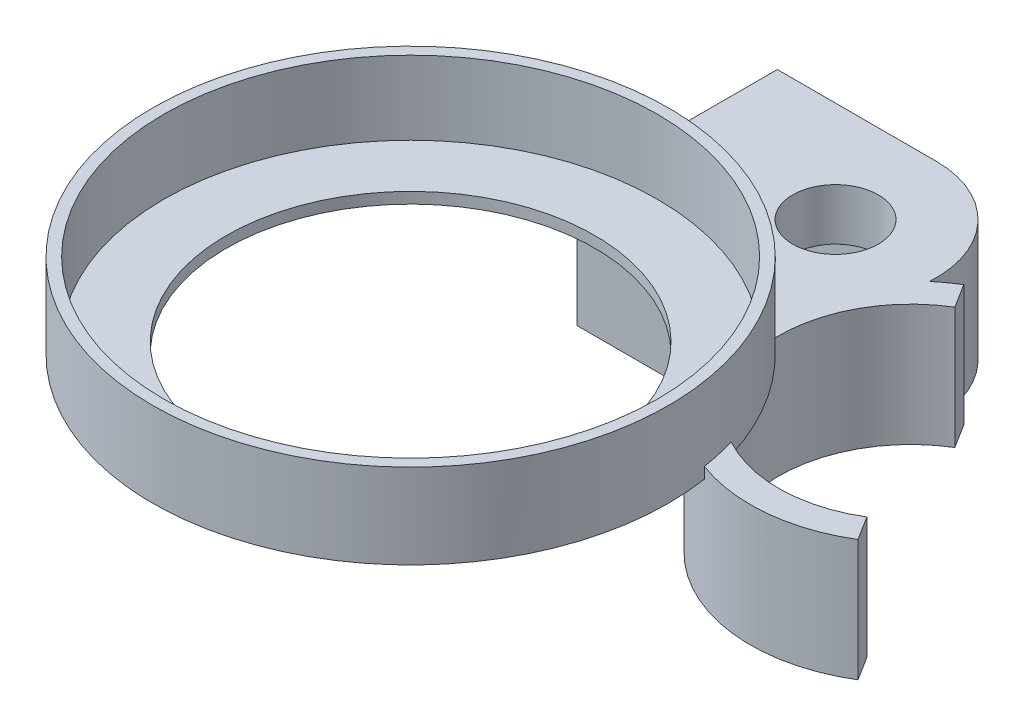
SolidWorks part; units mm, degrees
ref_plane "Front Plane" through (0, 0, 0) normal (0, 0, 1) x (1, 0, 0)
ref_plane "Top Plane" through (0, 0, 0) normal (0, 1, 0) x (1, 0, 0)
ref_plane "Right Plane" through (0, 0, 0) normal (1, 0, 0) x (0, 0, -1)
sketch "Sketch1" plane through (0, 0, 0) normal (0, 1, 0) x (1, 0, 0)
  line L1 (61.6703, 88.5071) -> (65.7389, 82.0027)
  line L2 (103.1428, 20.736) -> (107.2115, 14.2316)
  line L3 (-14.2234, 113.7805) -> (-14.2234, 68.5397)
  line L4 (-14.2234, 113.7805) -> (28.941, 113.7805)
  circle A0 centre (0, 0) radius 50
  arc A1 (-14.2234, 68.5397) -> (69.1989, 10.5601) centre (0, 0) ccw
  arc A2 (103.1428, 20.736) -> (67.0979, 19.9466) centre (84.4409, 51.3693) cw
  arc A3 (107.2115, 14.2316) -> (69.1989, 10.5601) centre (84.4409, 51.3693) cw
  arc A4 (56.2504, 84.5809) -> (61.6703, 88.5071) centre (84.4409, 51.3693) cw
  arc A5 (48.5626, 50.4151) -> (65.7389, 82.0027) centre (84.4409, 51.3693) cw
  arc A7 (56.2504, 84.5809) -> (28.941, 113.7805) centre (28.941, 86.4099) ccw
  arc A9 (67.0979, 19.9466) -> (48.5626, 50.4151) centre (0, 0) ccw
  circle A11 centre (28.941, 86.4099) radius 11.6151
  point P3 (27.4497, 84.5809)
  point P12 (55.3315, 95.0911)
  point P14 (28.3981, 84.5809)
  point P18 (56.888, 85.1117)
  dimension "D1" = 100
  dimension "D2" = 140
  dimension "D3" = 27.3706
extrude "Boss-Extrude1" add sketch "Sketch1" along normal blind 3
sketch "Sketch2" plane through (0, 3, 0) normal (0, 1, 0) x (1, 0, 0)
  circle A0 centre (0, 0) radius 67
  circle A2 centre (0, 0) radius 70
  dimension "D1" = 134
extrude "Boss-Extrude3" add sketch "Sketch2" along normal blind 20
sketch "Sketch4" plane through (0, 0, 0) normal (0, -1, 0) x (1, 0, 0)
  line L0 (107.2115, -14.2316) -> (103.1428, -20.736)
  line L1 (65.7389, -82.0027) -> (61.6703, -88.5071)
  line L5 (28.941, -113.7805) -> (-14.2234, -113.7805)
  line L6 (-14.2234, -113.7805) -> (-14.2234, -68.5397) construction
  line L7 (28.941, -113.7805) -> (-14.2234, -113.7805) construction
  line L8 (-14.2234, -113.7805) -> (-14.2234, -59.378)
  line L9 (-14.2234, -59.378) -> (41.6207, -59.378)
  arc A0 (103.1428, -20.736) -> (65.7389, -82.0027) centre (84.4409, -51.3693) ccw
  arc A1 (107.2115, -14.2316) -> (69.1989, -10.5601) centre (84.4409, -51.3693) ccw
  arc A3 (61.6703, -88.5071) -> (56.2504, -84.5809) centre (84.4409, -51.3693) cw
  circle A5 centre (28.941, -86.4099) radius 11.6151
  arc A6 (41.6207, -59.378) -> (69.1989, -10.5601) centre (84.4409, -51.3693) cw
  arc A8 (56.2504, -84.5809) -> (28.941, -113.7805) centre (28.941, -86.4099) cw
  point P5 (40.8782, -51.3693)
  point P8 (41.6207, -59.378)
extrude "Boss-Extrude6" add sketch "Sketch4" along normal blind 30
sketch "Sketch6" plane through (0, -30, 0) normal (0, -1, 0) x (1, 0, 0)
  line L0 (28.941, -104.5977) -> (-14.2234, -104.5977)
  line L2 (28.941, -68.2222) -> (-14.2234, -68.2222)
  line L3 (-14.2234, -68.2222) -> (-14.2234, -104.5977)
  arc A0 (28.941, -104.5977) -> (28.941, -68.2222) centre (28.941, -86.4099) ccw
  point P1 (0, 0)
  point P5 (28.941, -68.2222)
extrude "Cut-Extrude2" cut sketch "Sketch6" against normal blind 19
